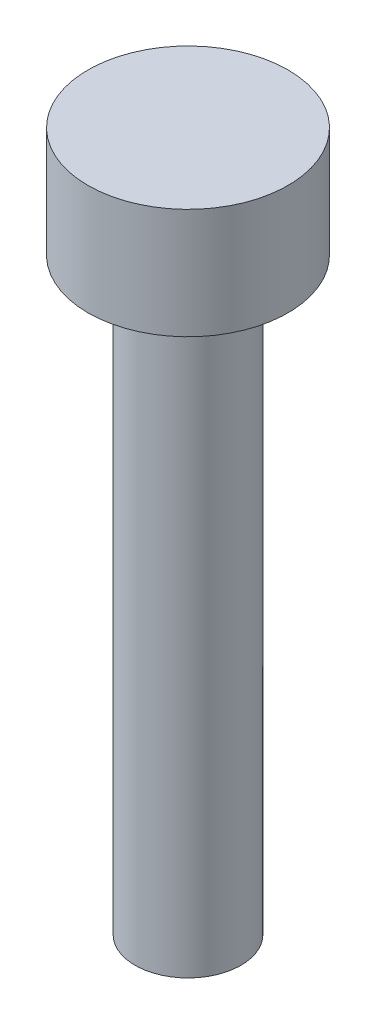
SolidWorks part; units mm, degrees
ref_plane "Front Plane" through (0, 0, 0) normal (0, 0, 1) x (1, 0, 0)
ref_plane "Top Plane" through (0, 0, 0) normal (0, 1, 0) x (1, 0, 0)
ref_plane "Right Plane" through (0, 0, 0) normal (1, 0, 0) x (0, 0, -1)
sketch "Sketch1" plane through (0, 0, 0) normal (0, 1, 0) x (1, 0, 0)
  circle A0 centre (0, 0) radius 2.72
  dimension "D1" = 5.44
extrude "Boss-Extrude1" add sketch "Sketch1" along normal blind 3
sketch "Sketch2" plane through (0, 0, 0) normal (0, -1, 0) x (1, 0, 0)
  circle A0 centre (0, 0) radius 1.44
  dimension "D1" = 2.88
extrude "Boss-Extrude2" add sketch "Sketch2" along normal blind 16
